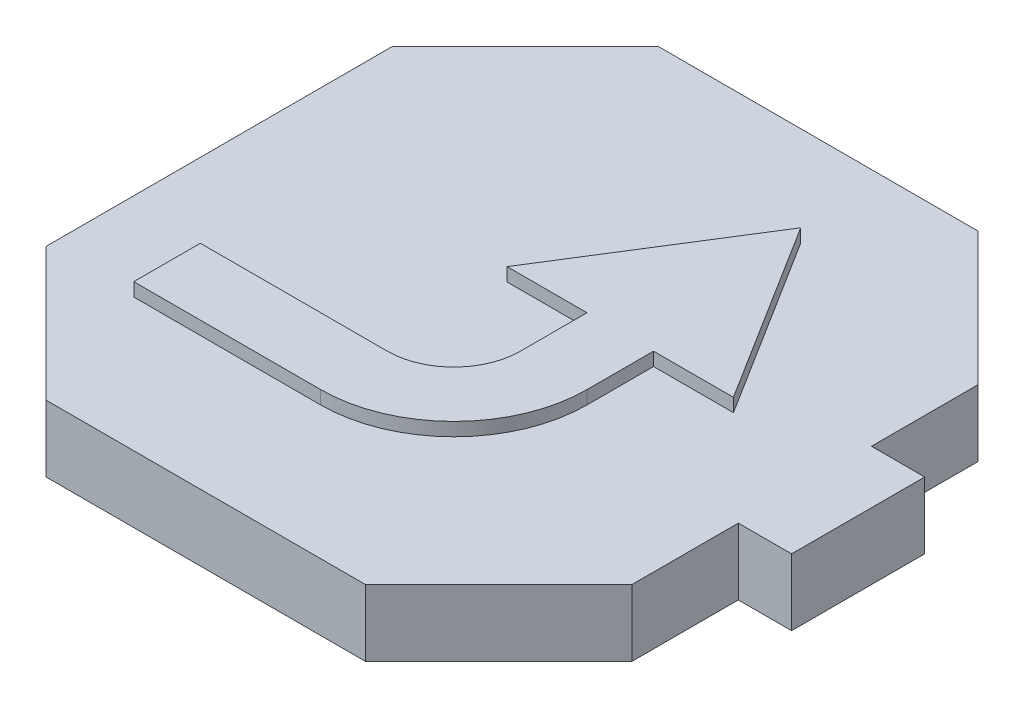
SolidWorks part; units mm, degrees
ref_plane "Plan de face" through (0, 0, 0) normal (0, 0, 1) x (1, 0, 0)
ref_plane "Plan de dessus" through (0, 0, 0) normal (0, 1, 0) x (1, 0, 0)
ref_plane "Plan de droite" through (0, 0, 0) normal (1, 0, 0) x (0, 0, -1)
sketch "Esquisse1" plane through (0, 0, 0) normal (0, 1, 0) x (1, 0, 0)
  line L0 (22, 13) -> (12.003, 23)
  line L1 (22, 13) -> (22, 5)
  line L2 (-22, -13) -> (-22, 13)
  line L3 (22, 5) -> (26, 5)
  line L4 (22, -5) -> (22, -13)
  line L5 (-22, -13) -> (22, 13) construction
  line L6 (-22, 13) -> (22, -13) construction
  line L7 (12.003, 23) -> (-12.003, 23)
  line L8 (-12.003, 23) -> (-22, 13)
  line L9 (-22, -13) -> (-12.003, -23)
  line L10 (-12.003, -23) -> (12.003, -23)
  line L11 (12.003, -23) -> (22, -13)
  line L12 (0, 23) -> (0, 0) construction
  line L13 (0, 0) -> (0, -23) construction
  line L14 (22, -5) -> (26, -5)
  line L15 (26, 5) -> (26, -5)
  point P1 (0, 0)
  dimension "D1" = 26
  dimension "D2" = 44
  dimension "D3" = 23
  dimension "D4" = 23
  dimension "D5" = 14.14
  dimension "D6" = 14.14
  dimension "D7" = 14.14
  dimension "D8" = 14.14
  dimension "D9" = 8
  dimension "D10" = 8
  dimension "D11" = 4
extrude "Boss.-Extru.1" add sketch "Esquisse1" along normal blind 5
sketch "Esquisse2" plane through (0, 5, 0) normal (0, 1, 0) x (1, 0, 0)
  line L0 (-15.4096, -8) -> (3.6319, -8)
  line L1 (3.6319, -8) -> (3.6319, 2)
  line L2 (3.6319, 2) -> (-2.3681, 2)
  line L3 (-2.3681, 2) -> (6.1319, 15.5554)
  line L4 (6.1319, 15.5554) -> (14.6319, 2)
  line L5 (14.6319, 2) -> (8.6319, 2)
  line L6 (8.6319, 2) -> (8.6319, -13)
  line L7 (8.6319, -13) -> (-15.4096, -13)
  line L8 (-15.4096, -13) -> (-15.4096, -8)
  line L9 (8.6319, -5.5) -> (3.6319, -5.5) construction
  line L10 (6.1319, 15.5554) -> (6.1319, -5.5) construction
  line L11 (-12.003, -23) -> (12.003, -23) construction
  dimension "D1" = 10
  dimension "D2" = 5
  dimension "D3" = 5
  dimension "D4" = 6
  dimension "D5" = 6
  dimension "D6" = 16
  dimension "D7" = 10
extrude "Boss.-Extru.2" add sketch "Esquisse2" along normal blind 1
sketch "Esquisse3" plane through (0, 0, 0) normal (0, -1, 0) x (1, 0, 0)
  line L0 (-12.003, 23) -> (12.003, 23) construction
  line L1 (-16, 17) -> (-10.8, 17)
  line L2 (-16, 17) -> (-16, 11.8)
  line L3 (-16, 11.8) -> (-10.8, 11.8)
  line L4 (-10.8, 17) -> (-10.8, 11.8)
  line L5 (-16, 17) -> (-10.8, 11.8) construction
  line L6 (-16, 11.8) -> (-10.8, 17) construction
  line L8 (-22, -13) -> (-22, 13) construction
  line L9 (12.003, -23) -> (-12.003, -23) construction
  line L10 (-16, -17) -> (-10.8, -17)
  line L11 (-16, -17) -> (-16, -11.8)
  line L12 (-16, -11.8) -> (-10.8, -11.8)
  line L13 (-10.8, -17) -> (-10.8, -11.8)
  line L14 (-16, -17) -> (-10.8, -11.8) construction
  line L15 (-16, -11.8) -> (-10.8, -17) construction
  line L16 (11.8, -11.8) -> (17, -11.8)
  line L17 (11.8, -11.8) -> (11.8, -17)
  line L18 (11.8, -17) -> (17, -17)
  line L19 (17, -11.8) -> (17, -17)
  line L20 (11.8, -11.8) -> (17, -17) construction
  line L21 (11.8, -17) -> (17, -11.8) construction
  line L22 (10.8, 11.8) -> (16, 11.8)
  line L23 (10.8, 11.8) -> (10.8, 17)
  line L24 (10.8, 17) -> (16, 17)
  line L25 (16, 11.8) -> (16, 17)
  line L26 (10.8, 11.8) -> (16, 17) construction
  line L27 (10.8, 17) -> (16, 11.8) construction
  line L28 (22, -5) -> (22, -13) construction
  line L29 (22, 13) -> (22, 5) construction
  line L31 (-2.5, -2.5) -> (2.5, -2.5)
  line L32 (-2.5, -2.5) -> (-2.5, 2.5)
  line L33 (-2.5, 2.5) -> (2.5, 2.5)
  line L34 (2.5, -2.5) -> (2.5, 2.5)
  line L35 (-2.5, -2.5) -> (2.5, 2.5) construction
  line L36 (-2.5, 2.5) -> (2.5, -2.5) construction
  point P0 (-13.4, 14.4)
  point P9 (-13.4, -14.4)
  point P14 (14.4, -14.4)
  point P19 (13.4, 14.4)
  point P30 (0, 0)
  dimension "D1" = 5.2
  dimension "D2" = 5.2
  dimension "D3" = 6
  dimension "D4" = 6
  dimension "D5" = 5.2
  dimension "D6" = 5.2
  dimension "D7" = 5.2
  dimension "D8" = 5.2
  dimension "D9" = 5.2
  dimension "D10" = 5.2
  dimension "D11" = 6
  dimension "D12" = 6
  dimension "D13" = 6
  dimension "D14" = 5
  dimension "D15" = 6
  dimension "D16" = 6
  dimension "D17" = 5
  dimension "D18" = 5
  dimension "D19" = 20.5
  dimension "D20" = 20.5
  dimension "D21" = 19.5
  dimension "D22" = 19.5
extrude "Enlèv. mat.-Extru.1" cut sketch "Esquisse3" against normal blind 4.8
fillet "Congé1" radius 10 1 edges at (8.6319, 5.5, 13)
fillet "Congé2" radius 5 1 edges at (3.6319, 5.5, 8)
